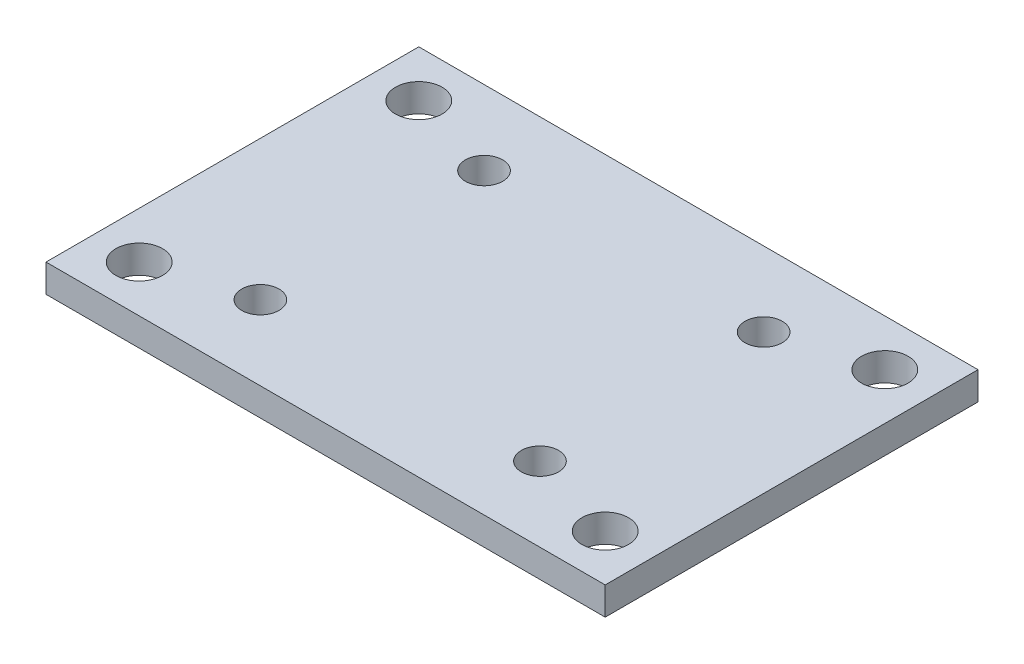
SolidWorks part; units mm, degrees
ref_plane "Front Plane" through (0, 0, 0) normal (0, 0, 1) x (1, 0, 0)
ref_plane "Top Plane" through (0, 0, 0) normal (0, 1, 0) x (1, 0, 0)
ref_plane "Right Plane" through (0, 0, 0) normal (1, 0, 0) x (0, 0, -1)
sketch "Sketch1" plane through (0, 0, 0) normal (0, 1, 0) x (1, 0, 0)
  line L1 (30, -20) -> (-30, -20)
  line L2 (30, -20) -> (30, 20)
  line L3 (30, 20) -> (-30, 20)
  line L4 (-30, -20) -> (-30, 20)
  line L5 (30, -20) -> (-30, 20) construction
  line L6 (30, 20) -> (-30, -20) construction
  point P0 (0, 0)
  dimension "D1" = 60
  dimension "D2" = 40
extrude "Boss-Extrude1" add sketch "Sketch1" along normal blind 3
sketch "Sketch2" plane through (0, 3, 0) normal (0, 1, 0) x (1, 0, 0)
  line L0 (-15, 12) -> (15, 12) construction
  line L1 (15, 12) -> (15, -12) construction
  circle A0 centre (-15, 12) radius 2
  circle A1 centre (15, 12) radius 2
  circle A2 centre (15, -12) radius 2
  circle A3 centre (-15, -12) radius 2
  dimension "D1" = 30
  dimension "D2" = 24
extrude "Cut-Extrude1" cut sketch "Sketch2" against normal blind 3
sketch "Sketch3" plane through (0, 3, 0) normal (0, 1, 0) x (1, 0, 0)
  line L0 (-25, 15) -> (-25, -15) construction
  line L1 (-25, -15) -> (25, -15) construction
  circle A0 centre (-25, 15) radius 2.5
  circle A1 centre (-25, -15) radius 2.5
  circle A2 centre (25, 15) radius 2.5
  circle A3 centre (25, -15) radius 2.5
  dimension "D1" = 50
  dimension "D2" = 30
extrude "Cut-Extrude2" cut sketch "Sketch3" against normal blind 3
